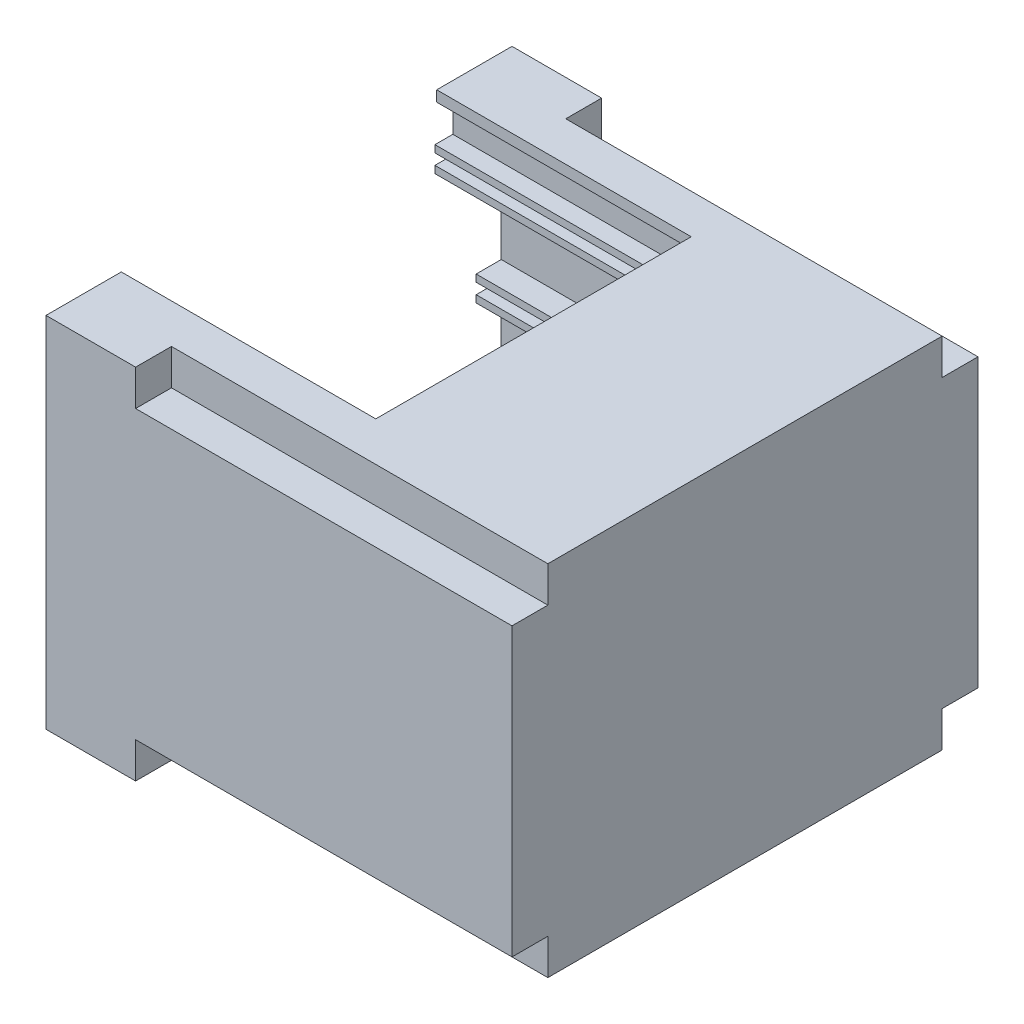
SolidWorks part; units mm, degrees
ref_plane "Front Plane" through (0, 0, 0) normal (0, 0, 1) x (1, 0, 0)
ref_plane "Top Plane" through (0, 0, 0) normal (0, 1, 0) x (1, 0, 0)
ref_plane "Right Plane" through (0, 0, 0) normal (1, 0, 0) x (0, 0, -1)
sketch "Sketch2" plane through (0, 0, 0) normal (0, 1, 0) x (1, 0, 0)
  line L1 (0, 0) -> (130, 0)
  line L2 (0, 0) -> (0, 130)
  line L3 (0, 130) -> (130, 130)
  line L4 (130, 0) -> (130, 130)
  dimension "D1" = 130
  dimension "D2" = 130
extrude "Boss-Extrude1" add sketch "Sketch2" along normal blind 100
sketch "Sketch3" plane through (0, 0, 0) normal (-1, 0, 0) x (0, 0, 1)
  line L0 (-130, 100) -> (0, 100) construction
  line L1 (-117, 13) -> (-13, 13)
  line L2 (-117, 13) -> (-117, 87)
  line L3 (-117, 87) -> (-13, 87)
  line L4 (-13, 13) -> (-13, 87)
  line L5 (0, 100) -> (0, 0) construction
  line L6 (-130, 0) -> (0, 0) construction
  line L7 (-130, 100) -> (-130, 0) construction
  dimension "D1" = 13
  dimension "D2" = 13
  dimension "D3" = 13
  dimension "D4" = 13
extrude "Cut-Extrude1" cut sketch "Sketch3" against normal blind 127
sketch "Sketch4" plane through (130, 0, 0) normal (1, 0, 0) x (0, 0, -1)
  line L1 (0, 100) -> (10, 100)
  line L2 (0, 100) -> (0, 90)
  line L3 (0, 90) -> (10, 90)
  line L4 (10, 100) -> (10, 90)
  line L5 (130, 100) -> (120, 100)
  line L6 (130, 100) -> (130, 90)
  line L7 (130, 90) -> (120, 90)
  line L8 (120, 100) -> (120, 90)
  line L9 (0, 0) -> (10, 0)
  line L10 (0, 0) -> (0, 10)
  line L11 (0, 10) -> (10, 10)
  line L12 (10, 0) -> (10, 10)
  line L13 (130, 0) -> (120, 0)
  line L14 (130, 0) -> (130, 10)
  line L15 (130, 10) -> (120, 10)
  line L16 (120, 0) -> (120, 10)
  dimension "D1" = 10
  dimension "D2" = 10
  dimension "D3" = 10
  dimension "D4" = 10
  dimension "D5" = 10
  dimension "D6" = 10
  dimension "D7" = 10
  dimension "D8" = 10
extrude "Cut-Extrude3" cut sketch "Sketch4" against normal blind 105
sketch "Sketch5" plane through (0, 0, 0) normal (-1, 0, 0) x (0, 0, 1)
  line L0 (-130, 100) -> (0, 100) construction
  line L1 (-117, 87) -> (-13, 87)
  line L2 (-117, 87) -> (-117, 97)
  line L3 (-117, 97) -> (-13, 97)
  line L4 (-13, 87) -> (-13, 97)
  line L5 (-117, 13) -> (-13, 13)
  line L6 (-117, 13) -> (-117, 3)
  line L7 (-117, 3) -> (-13, 3)
  line L8 (-13, 13) -> (-13, 3)
  line L9 (-130, 0) -> (0, 0) construction
  line L10 (0, 100) -> (0, 0) construction
  dimension "D1" = 3
  dimension "D2" = 3
  dimension "D3" = 13
  dimension "D4" = 13
extrude "Cut-Extrude4" cut sketch "Sketch5" against normal blind 127
sketch "Sketch6" plane through (0, 0, 0) normal (-1, 0, 0) x (0, 0, 1)
  line L0 (-117, 97) -> (-117, 3) construction
  line L1 (-117, 87) -> (-127, 87)
  line L2 (-117, 87) -> (-117, 13)
  line L3 (-117, 13) -> (-127, 13)
  line L4 (-127, 87) -> (-127, 13)
  line L5 (-13, 3) -> (-13, 97) construction
  line L6 (-13, 87) -> (-3, 87)
  line L7 (-13, 87) -> (-13, 13)
  line L8 (-13, 13) -> (-3, 13)
  line L9 (-3, 87) -> (-3, 13)
  line L10 (-130, 100) -> (-130, 0) construction
  line L11 (0, 100) -> (0, 0) construction
  line L12 (-130, 100) -> (0, 100) construction
  line L13 (-130, 0) -> (0, 0) construction
  dimension "D1" = 3
  dimension "D2" = 3
  dimension "D3" = 13
  dimension "D4" = 13
  dimension "D5" = 13
  dimension "D6" = 13
extrude "Cut-Extrude5" cut sketch "Sketch6" against normal blind 127
sketch "Sketch7" plane through (0, 0, 0) normal (-1, 0, 0) x (0, 0, 1)
  line L0 (0, 100) -> (0, 0) construction
  line L1 (-130, 0) -> (0, 0) construction
  line L2 (-130, 100) -> (-130, 0) construction
  line L3 (-130, 100) -> (0, 100) construction
  circle A0 centre (-124, 94) radius 1.75
  circle A1 centre (-6, 94) radius 1.75
  circle A2 centre (-124, 6) radius 1.75
  circle A3 centre (-6, 6) radius 1.75
  dimension "D3" = 3.5
  dimension "D6" = 3.5
  dimension "D9" = 3.5
  dimension "D12" = 3.5
  dimension "D1" = 6
  dimension "D2" = 6
  dimension "D4" = 6
  dimension "D5" = 6
  dimension "D7" = 6
  dimension "D8" = 6
  dimension "D10" = 6
  dimension "D11" = 6
extrude "Cut-Extrude6" cut sketch "Sketch7" against normal blind 20
sketch "Sketch8" plane through (0, 0, 0) normal (-1, 0, 0) x (0, 0, 1)
  line L1 (-117, 87) -> (-120, 87)
  line L2 (-117, 87) -> (-117, 90)
  line L3 (-117, 90) -> (-120, 90)
  line L4 (-120, 87) -> (-120, 90)
  line L5 (-13, 87) -> (-10, 87)
  line L6 (-13, 87) -> (-13, 90)
  line L7 (-13, 90) -> (-10, 90)
  line L8 (-10, 87) -> (-10, 90)
  line L9 (-117, 13) -> (-120, 13)
  line L10 (-117, 13) -> (-117, 10)
  line L11 (-117, 10) -> (-120, 10)
  line L12 (-120, 13) -> (-120, 10)
  line L13 (-13, 13) -> (-10, 13)
  line L14 (-13, 13) -> (-13, 10)
  line L15 (-13, 10) -> (-10, 10)
  line L16 (-10, 13) -> (-10, 10)
  dimension "D1" = 3
  dimension "D2" = 3
  dimension "D3" = 3
  dimension "D4" = 3
  dimension "D5" = 3
  dimension "D6" = 3
  dimension "D7" = 3
  dimension "D8" = 3
extrude "Cut-Extrude7" cut sketch "Sketch8" against normal blind 5
sketch "Sketch9" plane through (0, 3, 0) normal (0, 1, 0) x (1, 0, 0)
  line L1 (0, 117) -> (85, 117)
  line L2 (0, 117) -> (0, 57)
  line L3 (0, 57) -> (85, 57)
  line L4 (85, 117) -> (85, 57)
  dimension "D1" = 60
  dimension "D2" = 85
extrude "Boss-Extrude2" add sketch "Sketch9" along normal blind 15
sketch "Sketch11" plane through (0, 13, 0) normal (0, 1, 0) x (1, 0, 0)
  line L0 (0, 127) -> (0, 120) construction
  line L5 (85, 117) -> (0, 117)
  line L6 (85, 117) -> (85, 123)
  line L7 (85, 123) -> (0, 123)
  line L8 (0, 117) -> (0, 123)
  dimension "D1" = 6
extrude "Boss-Extrude5" add sketch "Sketch11" along normal blind 5
sketch "Sketch12" plane through (0, 18, 0) normal (0, 1, 0) x (1, 0, 0)
  line L0 (85, 57) -> (85, 123) construction
  line L1 (0, 123) -> (85, 123)
  line L2 (0, 123) -> (0, 120)
  line L3 (0, 120) -> (85, 120)
  line L4 (85, 123) -> (85, 120)
  dimension "D1" = 3
extrude "Cut-Extrude9" cut sketch "Sketch12" against normal blind 4
sketch "Sketch13" plane through (0, 18, 0) normal (0, 1, 0) x (1, 0, 0)
  line L0 (85, 57) -> (85, 120) construction
  line L1 (82, 117) -> (0, 117)
  line L2 (82, 117) -> (82, 60)
  line L3 (82, 60) -> (0, 60)
  line L4 (0, 117) -> (0, 60)
  line L5 (0, 57) -> (85, 57) construction
  line L6 (0, 120) -> (85, 120) construction
  line L7 (0, 120) -> (0, 57) construction
  dimension "D1" = 3
  dimension "D2" = 3
  dimension "D3" = 3
  dimension "D4" = 0
extrude "Cut-Extrude10" cut sketch "Sketch13" against normal blind 15
sketch "Sketch15" plane through (5, 0, 0) normal (-1, 0, 0) x (0, 0, 1)
  line L1 (-120, 13) -> (-117, 13)
  line L2 (-120, 13) -> (-120, 10)
  line L3 (-120, 10) -> (-117, 10)
  line L4 (-117, 13) -> (-117, 10)
extrude "Boss-Extrude7" add sketch "Sketch15" along normal blind 5
sketch "Sketch16" plane through (0, 0, -60) normal (0, 0, -1) x (-1, 0, 0)
  line L0 (0, 3) -> (0, 18) construction
  line L1 (-82, 18) -> (0, 18)
  line L2 (-82, 18) -> (-82, 16)
  line L3 (-82, 16) -> (0, 16)
  line L4 (0, 18) -> (0, 16)
  line L5 (-82, 3) -> (-82, 18) construction
  line L6 (-82, 13) -> (0, 13)
  line L7 (-82, 13) -> (-82, 11)
  line L8 (-82, 11) -> (0, 11)
  line L9 (0, 13) -> (0, 11)
  dimension "D1" = 2
  dimension "D2" = 2
  dimension "D3" = 3
extrude "Boss-Extrude8" add sketch "Sketch16" along normal blind 57
sketch "Sketch17" plane through (0, 18, 0) normal (0, 1, 0) x (1, 0, 0)
  line L0 (0, 120) -> (0, 57) construction
  line L1 (0, 112) -> (77, 112)
  line L2 (0, 112) -> (0, 65)
  line L3 (0, 65) -> (77, 65)
  line L4 (77, 112) -> (77, 65)
  line L5 (0, 57) -> (85, 57) construction
  line L6 (85, 57) -> (85, 120) construction
  line L7 (0, 120) -> (85, 120) construction
  dimension "D1" = 8
  dimension "D2" = 8
  dimension "D3" = 8
extrude "Cut-Extrude11" cut sketch "Sketch17" against normal blind 10
sketch "Sketch19" plane through (0, 0, -117) normal (0, 0, 1) x (1, 0, 0)
  line L1 (0, 11) -> (7, 11)
  line L2 (0, 11) -> (0, 9)
  line L3 (0, 9) -> (7, 9)
  line L4 (7, 11) -> (7, 9)
  line L5 (0, 13) -> (7, 13)
  line L6 (0, 13) -> (0, 14)
  line L7 (0, 14) -> (7, 14)
  line L8 (7, 13) -> (7, 14)
  dimension "D1" = 2
  dimension "D2" = 7
  dimension "D3" = 7
  dimension "D4" = 1
extrude "Boss-Extrude9" add sketch "Sketch19" along normal blind 1
sketch "Sketch21" plane through (0, 0, 0) normal (-1, 0, 0) x (0, 0, 1)
  line L0 (-130, 0) -> (0, 0) construction
  line L1 (-120, 13) -> (-117, 13)
  line L2 (-120, 13) -> (-120, 10)
  line L3 (-120, 10) -> (-117, 10)
  line L4 (-117, 13) -> (-117, 10)
  line L5 (-130, 100) -> (-130, 0) construction
  dimension "D1" = 3
  dimension "D2" = 3
  dimension "D3" = 10
  dimension "D4" = 10
extrude "Cut-Extrude15" cut sketch "Sketch21" against normal blind 5
sketch "Sketch22" plane through (127, 0, 0) normal (-1, 0, 0) x (0, 0, 1)
  line L0 (-127, 87) -> (-127, 13) construction
  line L1 (-127, 50) -> (-3, 50)
  line L2 (-127, 50) -> (-127, 43)
  line L3 (-127, 43) -> (-3, 43)
  line L4 (-3, 50) -> (-3, 43)
  line L5 (-3, 13) -> (-3, 87) construction
  line L6 (-65, 18) -> (-112, 18) construction
  dimension "D1" = 7
  dimension "D2" = 25
extrude "Boss-Extrude10" add sketch "Sketch22" along normal blind 127
sketch "Sketch23" plane through (0, 0, 0) normal (-1, 0, 0) x (0, 0, 1)
  line L0 (-3, 50) -> (-127, 50) construction
  line L1 (-125, 48) -> (-5, 48)
  line L2 (-125, 48) -> (-125, 45)
  line L3 (-125, 45) -> (-5, 45)
  line L4 (-5, 48) -> (-5, 45)
  line L5 (-130, 100) -> (-130, 0) construction
  dimension "D1" = 120
  dimension "D2" = 3
  dimension "D3" = 2
  dimension "D4" = 5
extrude "Cut-Extrude16" cut sketch "Sketch23" against normal blind 125
sketch "Sketch24" plane through (0, 50, 0) normal (0, 1, 0) x (1, 0, 0)
  line L0 (0, 3) -> (0, 127) construction
  line L1 (0, 120) -> (120, 120)
  line L2 (0, 120) -> (0, 10)
  line L3 (0, 10) -> (120, 10)
  line L4 (120, 120) -> (120, 10)
  line L5 (127, 3) -> (127, 127) construction
  line L6 (0, 127) -> (127, 127) construction
  line L7 (0, 3) -> (127, 3) construction
  dimension "D1" = 7
  dimension "D2" = 7
  dimension "D3" = 7
extrude "Cut-Extrude17" cut sketch "Sketch24" against normal blind 15
sketch "Sketch25" plane through (0, 100, 0) normal (0, 1, 0) x (1, 0, 0)
  line L0 (0, 130) -> (0, 0) construction
  line L1 (0, 109) -> (71, 109)
  line L2 (0, 109) -> (0, 21)
  line L3 (0, 21) -> (71, 21)
  line L4 (71, 109) -> (71, 21)
  line L6 (25, 120) -> (130, 120) construction
  dimension "D1" = 71
  dimension "D2" = 88
  dimension "D3" = 11
extrude "Cut-Extrude18" cut sketch "Sketch25" against normal blind 15
sketch "Sketch27" plane through (127, 0, 0) normal (-1, 0, 0) x (0, 0, 1)
  line L0 (-13, 97) -> (-117, 97) construction
  line L1 (-116.5, 97) -> (-13.5, 97)
  line L2 (-116.5, 97) -> (-116.5, 80)
  line L3 (-116.5, 80) -> (-13.5, 80)
  line L4 (-13.5, 97) -> (-13.5, 80)
  line L5 (-117, 97) -> (-117, 87) construction
  dimension "D1" = 103
  dimension "D2" = 0.5
  dimension "D3" = 17
extrude "Boss-Extrude11" add sketch "Sketch27" along normal blind 127
sketch "Sketch28" plane through (0, 0, 0) normal (-1, 0, 0) x (0, 0, 1)
  line L0 (-21, 97) -> (-109, 97) construction
  line L1 (-113.5, 85) -> (-16.5, 85)
  line L2 (-113.5, 85) -> (-113.5, 82)
  line L3 (-113.5, 82) -> (-16.5, 82)
  line L4 (-16.5, 85) -> (-16.5, 82)
  line L5 (-113.5, 97) -> (-16.5, 97)
  line L6 (-113.5, 97) -> (-113.5, 87)
  line L7 (-113.5, 87) -> (-16.5, 87)
  line L8 (-16.5, 97) -> (-16.5, 87)
  line L9 (-116.5, 80) -> (-13.5, 80) construction
  line L10 (-116.5, 97) -> (-116.5, 80) construction
  line L11 (-13.5, 80) -> (-13.5, 97) construction
  line L12 (-116.5, 97) -> (-116.5, 80) construction
  dimension "D1" = 10
  dimension "D2" = 0
  dimension "D3" = 2
  dimension "D4" = 3
  dimension "D5" = 3
  dimension "D6" = 3
  dimension "D7" = 3
  dimension "D8" = 3
extrude "Cut-Extrude19" cut sketch "Sketch28" against normal blind 120
sketch "Sketch29" plane through (0, 80, 0) normal (0, -1, 0) x (1, 0, 0)
  line L0 (0, -116.5) -> (127, -116.5) construction
  line L1 (127, -13.5) -> (123, -13.5)
  line L2 (127, -13.5) -> (127, -116.5)
  line L3 (127, -116.5) -> (123, -116.5)
  line L4 (123, -13.5) -> (123, -116.5)
  line L5 (0, -116.5) -> (0, -13.5) construction
  dimension "D1" = 123
extrude "Cut-Extrude20" cut sketch "Sketch29" against normal blind 17
sketch "Sketch30" plane through (0, 87, 0) normal (0, 1, 0) x (1, 0, 0)
  line L0 (0, 113.5) -> (0, 16.5) construction
  line L1 (0, 108.5) -> (115, 108.5)
  line L2 (0, 108.5) -> (0, 21.5)
  line L3 (0, 21.5) -> (115, 21.5)
  line L4 (115, 108.5) -> (115, 21.5)
  line L5 (120, 113.5) -> (0, 113.5) construction
  line L6 (120, 16.5) -> (0, 16.5) construction
  line L7 (120, 113.5) -> (120, 16.5) construction
  dimension "D1" = 5
  dimension "D2" = 5
  dimension "D3" = 5
extrude "Cut-Extrude21" cut sketch "Sketch30" against normal blind 17
